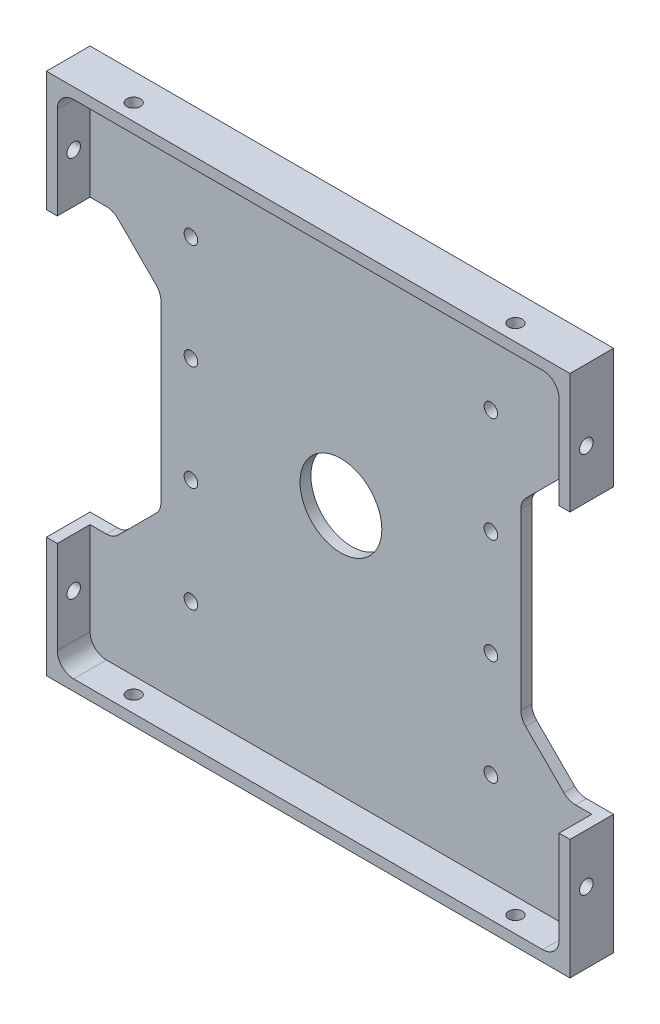
SolidWorks part; units mm, degrees
material "6061-T6 (SS)"
ref_plane "Front" through (0, 0, 0) normal (0, 0, 1) x (1, 0, 0)
ref_plane "Top" through (0, 0, 0) normal (0, 1, 0) x (1, 0, 0)
ref_plane "Right" through (0, 0, 0) normal (1, 0, 0) x (0, 0, -1)
sketch "Sketch1" plane through (0, 0, 0) normal (0, 0, 1) x (1, 0, 0)
  line L1 (-48, -48) -> (48, -48)
  line L2 (-48, -48) -> (-48, 48)
  line L3 (-48, 48) -> (48, 48)
  line L4 (48, -48) -> (48, 48)
  line L5 (-48, -48) -> (48, 48) construction
  line L6 (-48, 48) -> (48, -48) construction
  point P0 (0, 0)
  dimension "D1" = 96
  dimension "D2" = 96
extrude "Boss-Extrude1" add sketch "Sketch1" along normal blind 8
sketch "Sketch2" plane through (0, 0, 8) normal (0, 0, 1) x (1, 0, 0)
  line L1 (46, -46) -> (-46, -46)
  line L2 (46, -46) -> (46, 46)
  line L3 (46, 46) -> (-46, 46)
  line L4 (-46, -46) -> (-46, 46)
  line L5 (46, -46) -> (-46, 46) construction
  line L6 (46, 46) -> (-46, -46) construction
  point P0 (0, 0)
  dimension "D1" = 92
  dimension "D2" = 92
extrude "Component Platform" cut sketch "Sketch2" against normal blind 6
sketch "Sketch3" plane through (0, 0, 2) normal (0, 0, 1) x (1, 0, 0)
  line L1 (-40.8787, -25.1213) -> (-33.8787, -18.1213)
  line L2 (-40.8787, 25.1213) -> (-33.8787, 18.1213)
  line L3 (-33, -16) -> (-33, 16)
  line L4 (-48, -26) -> (-43, -26)
  line L7 (-48, 48) -> (-48, -48) construction
  line L8 (0, -56.7987) -> (0, 73.4321) construction
  line L9 (46, -46) -> (-57.8147, 57.8147) construction
  line L18 (46, 46) -> (-68.5705, -68.5705) construction
  line L23 (-48, 26) -> (-43, 26)
  line L26 (-48, -26) -> (-48, 26)
  line L28 (-48, -48) -> (48, -48) construction
  line L29 (48, -26) -> (48, 26)
  line L30 (48, 26) -> (43, 26)
  line L31 (40.8787, 25.1213) -> (33.8787, 18.1213)
  line L32 (33, -16) -> (33, 16)
  line L33 (40.8787, -25.1213) -> (33.8787, -18.1213)
  line L34 (48, -26) -> (43, -26)
  arc A3 (-33.8787, -18.1213) -> (-33, -16) centre (-36, -16) ccw
  arc A4 (-33.8787, 18.1213) -> (-33, 16) centre (-36, 16) cw
  arc A13 (-40.8787, -25.1213) -> (-43, -26) centre (-43, -23) cw
  arc A15 (-40.8787, 25.1213) -> (-43, 26) centre (-43, 23) ccw
  arc A17 (40.8787, 25.1213) -> (43, 26) centre (43, 23) cw
  arc A18 (33.8787, 18.1213) -> (33, 16) centre (36, 16) ccw
  arc A19 (33.8787, -18.1213) -> (33, -16) centre (36, -16) cw
  arc A20 (40.8787, -25.1213) -> (43, -26) centre (43, -23) ccw
  point P0 (-48, 0)
  point P37 (-48, 0)
  dimension "D2" = 3
  dimension "D3" = 3
  dimension "D4" = 15
  dimension "D6" = 3
  dimension "D7" = 3
  dimension "D8" = 135
  dimension "D5" = 52
  dimension "D9" = 135
  dimension "D10" = 5
  dimension "D11" = 5
  dimension "D12" = 48
extrude "Cable Slots" cut sketch "Sketch3" against normal mid plane 12
sketch "Sketch4" plane through (0, 0, 2) normal (0, 0, 1) x (1, 0, 0)
  circle A0 centre (0, 0) radius 7.5
  dimension "D1" = 15
extrude "Center Mass Cut" cut sketch "Sketch4" against normal blind 6
ref_plane "Center Y-Plane" through (0, 0, 0) normal (1, 0, 0) x (0, 0, -1)
ref_plane "Center X-Plane" through (0, 0, 0) normal (0, -1, 0) x (-1, 0, 0)
fillet "Inner Corner Fillets" radius 3 4 edges at (46, -46, 5) (-46, -46, 5) (46, 46, 5) (-46, 46, 5)
sketch "Sketch8" plane through (48, 0, 0) normal (1, 0, 0) x (0, 0, -1)
  line L0 (-5, -48) -> (-5, 48) construction
  line L1 (-8, -48) -> (0, -48) construction
  line L2 (-8, 48) -> (0, 48) construction
  line L3 (-8, -48) -> (-8, -26) construction
  dimension "D1" = 3
hole_wizard "M3x0.5 Tapped Hole1" positions "Sketch9" profile "Sketch10" tap size "M3x0.5" standard "ANSI Metric"
sketch "Sketch9" plane through (48, 0, 0) normal (1, 0, 0) x (0, 0, -1)
  line L0 (-5, -48) -> (-5, 48) construction
  point P0 (-5, -35)
  point P4 (-5, 35)
  dimension "D1" = 70
  dimension "D2" = 35
sketch "Sketch10" plane through (48, -35, 5) normal (0, 1, 0) x (0, 0, -1)
  line L0 (0, 0) -> (0, 10.7511)
  line L1 (0, 10.7511) -> (1.25, 10)
  line L2 (1.25, 10) -> (1.25, 0)
  line L5 (1.25, 0) -> (0, 0)
  line L10 (0, 10.7511) -> (-1.25, 10) construction
  line L11 (0, -6.35) -> (0, 107.95) construction
  dimension "Tap Drill Dia." = 2.5
  dimension "Tap Drill Depth" = 10
  dimension "Drill Angle" = 118
sketch "Sketch11" plane through (0, -48, 0) normal (0, -1, 0) x (-1, 0, 0)
  line L0 (48, -5) -> (-48.0639, -5) construction
  line L1 (48, -8) -> (48, 0) construction
  line L2 (48, -8) -> (-48, -8) construction
  dimension "D1" = 3
hole_wizard "M3x0.5 Tapped Hole2" positions "Sketch12" profile "Sketch13" tap size "M3x0.5" standard "ANSI Metric"
sketch "Sketch12" plane through (0, -48, 0) normal (0, -1, 0) x (-1, 0, 0)
  line L0 (48, -5) -> (-48.0639, -5) construction
  point P0 (35, -5)
  point P4 (-35, -5)
  dimension "D1" = 70
  dimension "D2" = 35
sketch "Sketch13" plane through (-35, -48, 5) normal (1, 0, 0) x (0, 0, -1)
  line L0 (0, 0) -> (0, 10.7511)
  line L1 (0, 10.7511) -> (1.25, 10)
  line L2 (1.25, 10) -> (1.25, 0)
  line L5 (1.25, 0) -> (0, 0)
  line L10 (0, 10.7511) -> (-1.25, 10) construction
  line L11 (0, -6.35) -> (0, 107.95) construction
  dimension "Tap Drill Dia." = 2.5
  dimension "Tap Drill Depth" = 10
  dimension "Drill Angle" = 118
mirror "Mirror1" about plane through (0, 0, 0) normal (1, 0, 0) of "M3x0.5 Tapped Hole1"
mirror "Mirror2" about plane through (0, 0, 0) normal (0, -1, 0) of "M3x0.5 Tapped Hole2"
sketch "Sketch14" plane through (0, 0, 2) normal (0, 0, 1) x (1, 0, 0)
  line L2 (-34.3786, 28.95) -> (20.4987, 28.95) construction
  line L4 (-27.5, 33.479) -> (-27.5, -23.7116) construction
  line L5 (0, 0) -> (0, 28.95) construction
  point P7 (-27.5, 28.95)
  point P8 (-27.5, -9.65)
  point P9 (-27.5, 9.65)
  point P11 (-27.5, -28.95)
  point P13 (27.5, -28.95)
  point P14 (27.5, -9.65)
  point P15 (27.5, 9.65)
  point P16 (27.5, 28.95)
  dimension "D1" = 27.5
  dimension "D2" = 28.95
  dimension "D3" = 19.3
  dimension "D4" = 19.3
  dimension "D5" = 19.3
hole_wizard "M3x0.5 Tapped Hole3" positions "Sketch15" profile "Sketch17" tap size "M3x0.5" standard "ANSI Metric" end condition through all
sketch "Sketch15" plane through (0, 0, 2) normal (0, 0, 1) x (1, 0, 0)
  point P0 (-27.5, 28.95)
  point P3 (-27.5, 9.65)
  point P6 (-27.5, -9.65)
  point P9 (-27.5, -28.95)
  point P12 (27.5, -28.95)
  point P15 (27.5, -9.65)
  point P18 (27.5, 9.65)
  point P21 (27.5, 28.95)
sketch "Sketch17" plane through (-27.5, 28.95, 2) normal (1, 0, 0) x (0, -1, 0)
  line L0 (0, 0) -> (0, 2)
  line L1 (0, 2) -> (1.25, 2)
  line L2 (1.25, 2) -> (1.25, 0)
  line L5 (1.25, 0) -> (0, 0)
  line L11 (0, -6.35) -> (0, 107.95) construction
  dimension "Thru Tap Drill Dia." = 2.5
  dimension "Thru Tap Drill Depth" = 2
cosmetic thread "Hole Thread1" parameters "D2"=3
cosmetic thread "Hole Thread2" parameters "D2"=3
cosmetic thread "Hole Thread3" parameters "D2"=3
cosmetic thread "Hole Thread4" parameters "D2"=3
cosmetic thread "Hole Thread5" parameters "D2"=3
cosmetic thread "Hole Thread6" parameters "D2"=3
cosmetic thread "Hole Thread7" parameters "D2"=3
cosmetic thread "Hole Thread8" parameters "D2"=3
